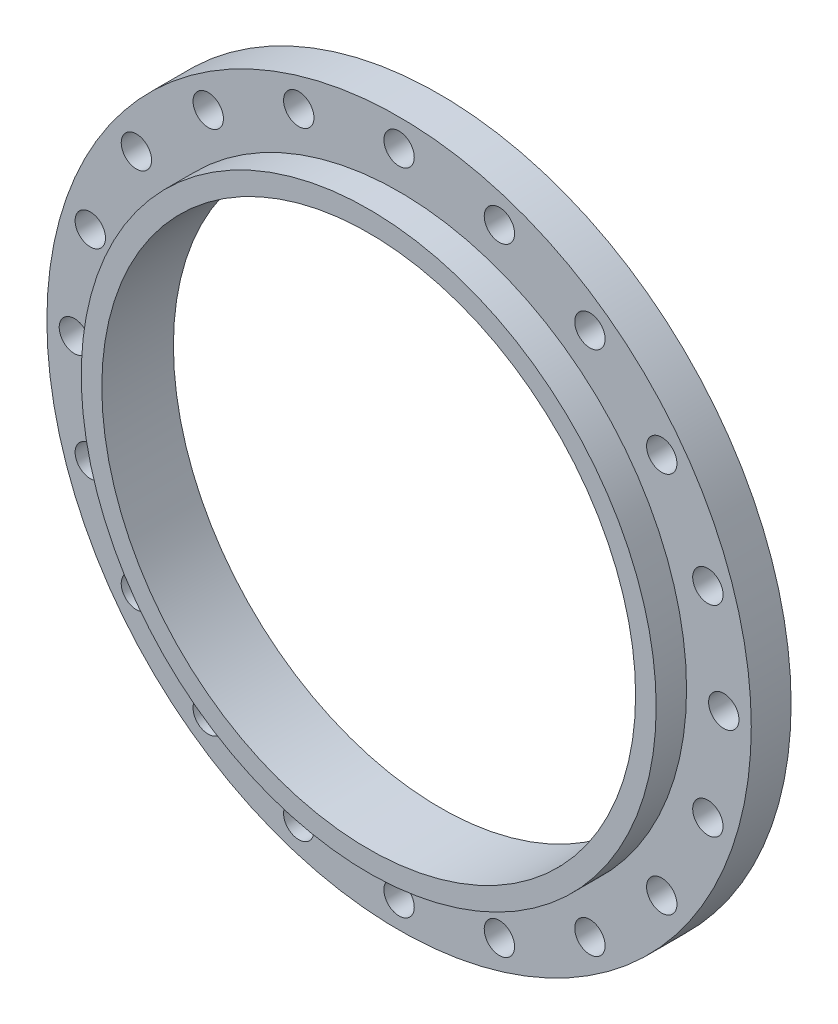
SolidWorks part; units mm, degrees
ref_plane "Front Plane" through (0, 0, 0) normal (0, 0, 1) x (1, 0, 0)
ref_plane "Top Plane" through (0, 0, 0) normal (0, 1, 0) x (1, 0, 0)
ref_plane "Right Plane" through (0, 0, 0) normal (1, 0, 0) x (0, 0, -1)
sketch "Sketch2" plane through (0, 0, 0) normal (0, 0, 1) x (1, 0, 0)
  circle A0 centre (0, 0) radius 16
  dimension "D1" = 32
extrude "Boss-Extrude1" add sketch "Sketch2" along normal blind 1.81 contours A0
sketch "Sketch3" plane through (0, 0, 0) normal (0, 0, 1) x (1, 0, 0)
  circle A0 centre (0, 0) radius 13.06
  dimension "D1" = 26.12
extrude "Boss-Extrude2" add sketch "Sketch3" along normal blind 3.19
sketch "Sketch4" plane through (0, 0, 0) normal (0, 0, 1) x (1, 0, 0)
  circle A0 centre (0, 0) radius 13.625
  dimension "D1" = 27.25
extrude "Boss-Extrude3" add sketch "Sketch4" against normal blind 0.0625
sketch "Sketch5" plane through (0, 0, 0) normal (0, 0, 1) x (1, 0, 0)
  circle A0 centre (0, 0) radius 12.125
  dimension "D1" = 24.25
extrude "Cut-Extrude1" cut sketch "Sketch5" against normal blind 4.0625 and the other way blind 56
sketch "Sketch6" plane through (0, 0, 0) normal (0, 0, 1) x (1, 0, 0)
  circle A0 centre (0, 14.75) radius 0.69
  dimension "D1" = 1.38
  dimension "D2" = 14.75
extrude "Cut-Extrude2" cut sketch "Sketch6" along normal blind 2.0625
sketch "Sketch7" plane through (0, 0, 0) normal (0, 1, 0) x (1, 0, 0)
  line L0 (0, 0) -> (0, -3.3659) construction
pattern_circular "CirPattern1" count 20 over 360 about axis through (0, 0, 0) along (0, 0, 1) of "Cut-Extrude2"
scale "Scale1" scale about centroid uniform scaling yes scale factor 25.4
